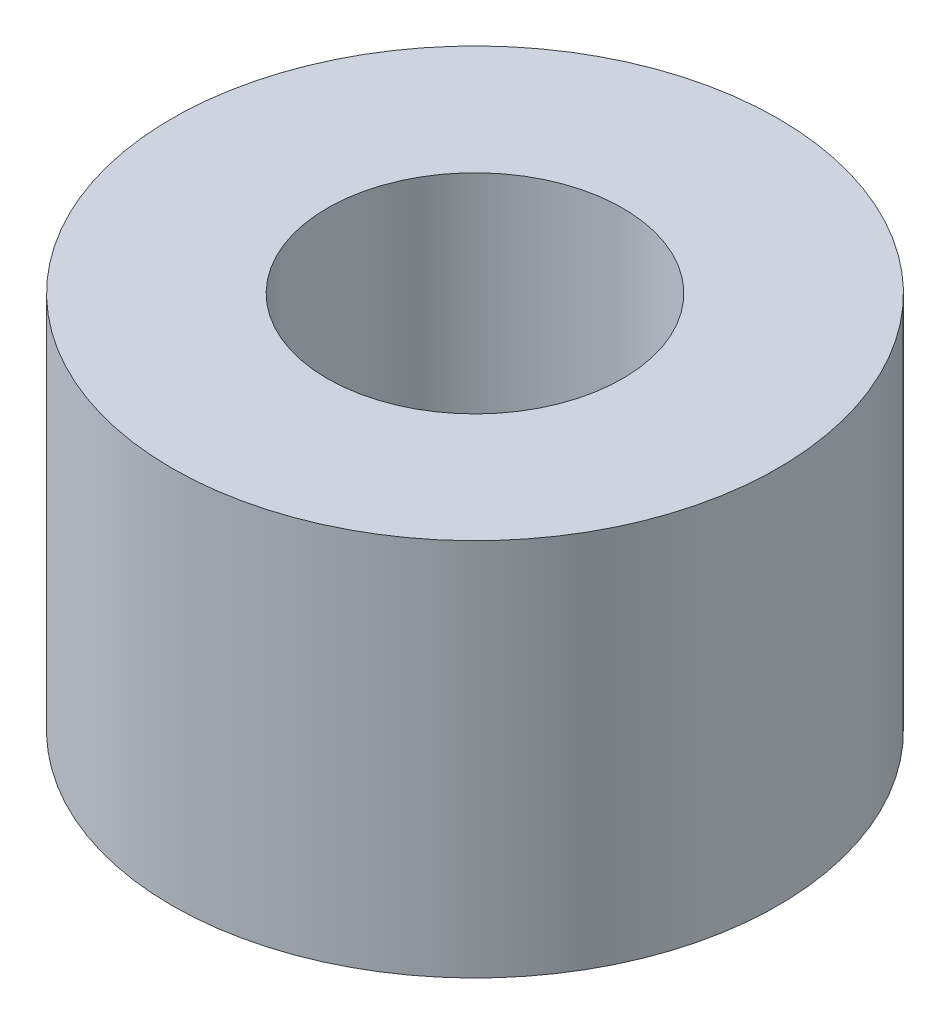
SolidWorks part; units mm, degrees
ref_plane "前视基准面" through (0, 0, 0) normal (0, 0, 1) x (1, 0, 0)
ref_plane "上视基准面" through (0, 0, 0) normal (0, 1, 0) x (1, 0, 0)
ref_plane "右视基准面" through (0, 0, 0) normal (1, 0, 0) x (0, 0, -1)
sketch "草图1" plane through (0, 0, 0) normal (0, 1, 0) x (1, 0, 0)
  circle A0 centre (0, 0) radius 1.95
  circle A1 centre (0, 0) radius 4
  dimension "D1" = 3.9
  dimension "D2" = 8
extrude "凸台-拉伸1" add sketch "草图1" along normal blind 5
